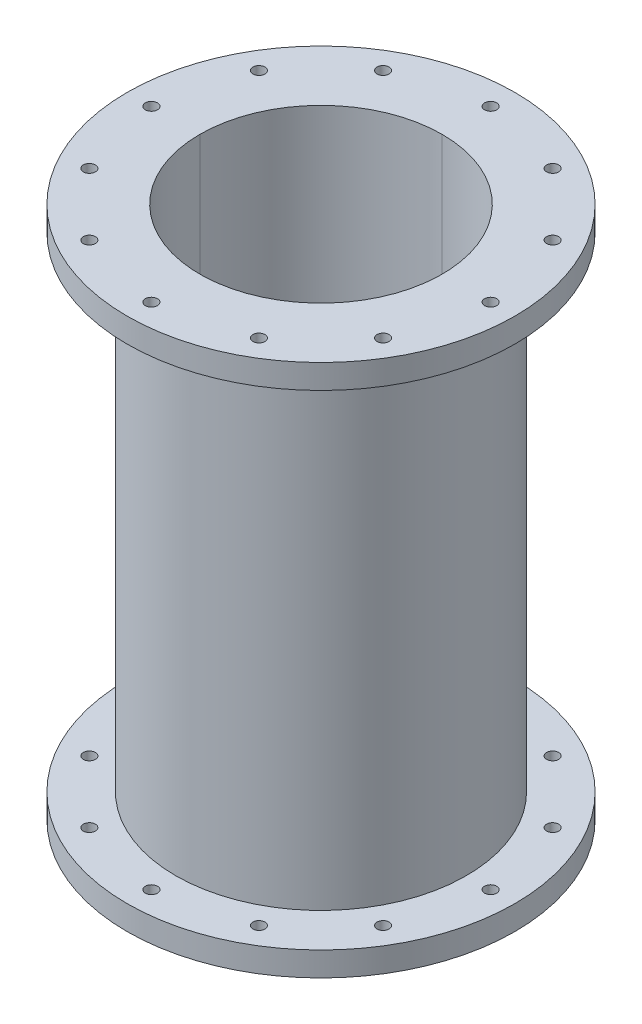
SolidWorks part; units mm, degrees
material "Plain Carbon Steel"
ref_plane "Front Plane" through (0, 0, 0) normal (0, 0, 1) x (1, 0, 0)
ref_plane "Top Plane" through (0, 0, 0) normal (0, 1, 0) x (1, 0, 0)
ref_plane "Right Plane" through (0, 0, 0) normal (1, 0, 0) x (0, 0, -1)
sketch "Sketch1" plane through (0, 0, 0) normal (0, 1, 0) x (1, 0, 0)
  line L0 (0, 101.6) -> (0, -101.6)
  line L1 (-101.6, 0) -> (101.6, 0)
  line L2 (0, 0) -> (0, 88.9) construction
  circle A0 centre (0, 0) radius 63.5
  circle A1 centre (0, 0) radius 76.2
  circle A2 centre (0, 0) radius 88.9
  circle A3 centre (0, 0) radius 101.6
  circle A4 centre (0, 88.9) radius 3.175
  circle A6 centre (88.9, 0) radius 3.175
  circle A7 centre (0, 0) radius 88.9
  circle A8 centre (0, 0) radius 88.9
  circle A9 centre (0, 0) radius 88.9
  circle A10 centre (0, 0) radius 88.9
  circle A11 centre (0, 0) radius 88.9
  circle A12 centre (0, 0) radius 88.9
  circle A13 centre (0, 0) radius 88.9
  circle A14 centre (0, 0) radius 88.9
  circle A15 centre (0, 0) radius 88.9
  circle A16 centre (0, 0) radius 88.9
  circle A17 centre (0, 0) radius 88.9
  circle A18 centre (44.45, 76.9897) radius 3.175
  circle A19 centre (76.9897, 44.45) radius 3.175
  circle A20 centre (88.9, 0) radius 3.175
  circle A21 centre (76.9897, -44.45) radius 3.175
  circle A22 centre (44.45, -76.9897) radius 3.175
  circle A23 centre (0, -88.9) radius 3.175
  circle A24 centre (-44.45, -76.9897) radius 3.175
  circle A25 centre (-76.9897, -44.45) radius 3.175
  circle A26 centre (-88.9, 0) radius 3.175
  circle A27 centre (-76.9897, 44.45) radius 3.175
  circle A28 centre (-44.45, 76.9897) radius 3.175
  point P39 (0, 0)
  dimension "D1" = 127
  dimension "D2" = 152.4
  dimension "D3" = 177.8
  dimension "D4" = 203.2
  dimension "D5" = 6.35
  dimension "D6" = 6.35
  dimension "D9" = 88.9
  dimension "D7" = 12
  dimension "D8" = 12
extrude "Boss-Extrude1" add sketch "Sketch1" along normal mid plane 279.4 contours L0 A0 L1 | L1 A0 L0 | L1 A0 L0 | L0 A2 L1 A1 | L0 A3 L1 A2 | L0 A1 L1 A0 | L1 A2 L0 A1 | L1 A1 L0 A0 | L1 A3 L0 A2 | L1 A3 L0 A2 | L1 A2 L0 A1 | L1 A1 L0 A0 | L0 A1 L1 A0 | L0 A2 L1 A1 | L0 A3 L1 A2
ref_plane "Plane1" through (0, 0, 0) normal (0, 1, 0) x (1, 0, 0)
sketch "Sketch5" plane through (0, 0, 0) normal (0, 1, 0) x (1, 0, 0)
  circle A0 centre (0, 0) radius 76.2
  arc A1 (-63.5, 0) -> (0, 63.5) centre (0, 0) ccw construction
  circle A2 centre (0, 0) radius 101.6
  circle A3 centre (0, 0) radius 101.6
  arc A4 (-63.5, 0) -> (0, 63.5) centre (0, 0) ccw
  arc A5 (0, 63.5) -> (-63.5, 0) centre (0, 0) ccw construction
  arc A6 (0, 63.5) -> (-63.5, 0) centre (0, 0) ccw
  circle A7 centre (0, 88.9) radius 3.175 construction
  circle A8 centre (0, 88.9) radius 3.175
  circle A9 centre (-76.9897, 44.45) radius 3.175 construction
  circle A10 centre (-76.9897, 44.45) radius 3.175
  circle A11 centre (44.45, 76.9897) radius 3.175 construction
  circle A12 centre (76.9897, 44.45) radius 3.175 construction
  circle A13 centre (88.9, 0) radius 3.175 construction
  circle A14 centre (76.9897, -44.45) radius 3.175 construction
  circle A15 centre (44.45, -76.9897) radius 3.175 construction
  circle A16 centre (0, -88.9) radius 3.175 construction
  circle A17 centre (-44.45, -76.9897) radius 3.175 construction
  circle A18 centre (-76.9897, -44.45) radius 3.175 construction
  circle A19 centre (-88.9, 0) radius 3.175 construction
  circle A20 centre (-44.45, 76.9897) radius 3.175 construction
  circle A21 centre (44.45, 76.9897) radius 3.175
  circle A22 centre (76.9897, 44.45) radius 3.175
  circle A23 centre (88.9, 0) radius 3.175
  circle A24 centre (76.9897, -44.45) radius 3.175
  circle A25 centre (44.45, -76.9897) radius 3.175
  circle A26 centre (0, -88.9) radius 3.175
  circle A27 centre (-44.45, -76.9897) radius 3.175
  circle A28 centre (-76.9897, -44.45) radius 3.175
  circle A29 centre (-88.9, 0) radius 3.175
  circle A30 centre (-44.45, 76.9897) radius 3.175
  dimension "D1" = 152.4
  dimension "D2" = 0
extrude "Cut-Extrude3" cut sketch "Sketch5" against normal mid plane 254 contours A3 A30 A29 A28 A27 A26 A25 A24 A23 A22 A21 A10 A8 A0
